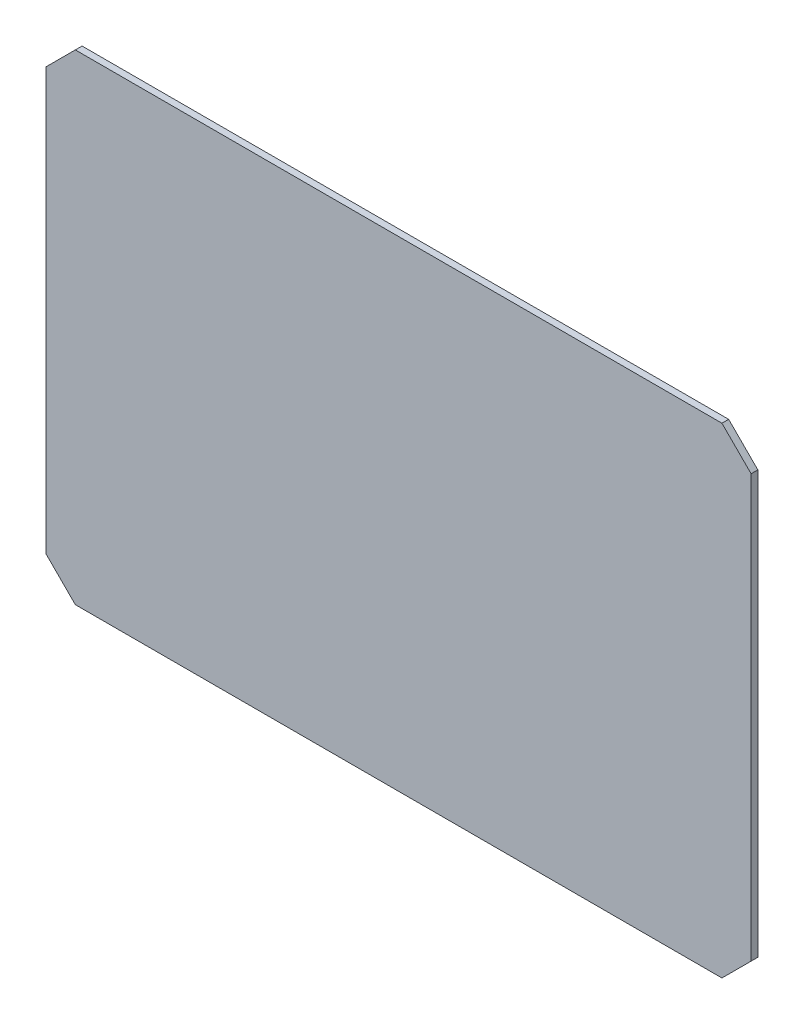
SolidWorks part; units mm, degrees
ref_plane "Front Plane" through (0, 0, 0) normal (0, 0, 1) x (1, 0, 0)
ref_plane "Top Plane" through (0, 0, 0) normal (0, 1, 0) x (1, 0, 0)
ref_plane "Right Plane" through (0, 0, 0) normal (1, 0, 0) x (0, 0, -1)
sketch "Sketch1" plane through (0, 0, 0) normal (0, 0, 1) x (1, 0, 0)
  line L0 (0, 199.848) -> (0, -197.7062) construction
  line L1 (144, -107) -> (-144, -107)
  line L2 (157, -94) -> (157, 94)
  line L3 (144, 107) -> (-144, 107)
  line L4 (-157, -94) -> (-157, 94)
  line L5 (157, -107) -> (-157, 107) construction
  line L6 (157, 107) -> (-157, -107) construction
  line L7 (-251.8325, 0) -> (224.177, 0) construction
  line L8 (-157, 94) -> (-144, 107)
  line L13 (157, 94) -> (144, 107)
  line L14 (157, -94) -> (144, -107)
  line L19 (-157, -94) -> (-144, -107)
  point P0 (0, 0)
  dimension "D1" = 314
  dimension "D2" = 214
  dimension "D3" = 13
  dimension "D4" = 13
extrude "Extrude1" add sketch "Sketch1" along normal blind 3
